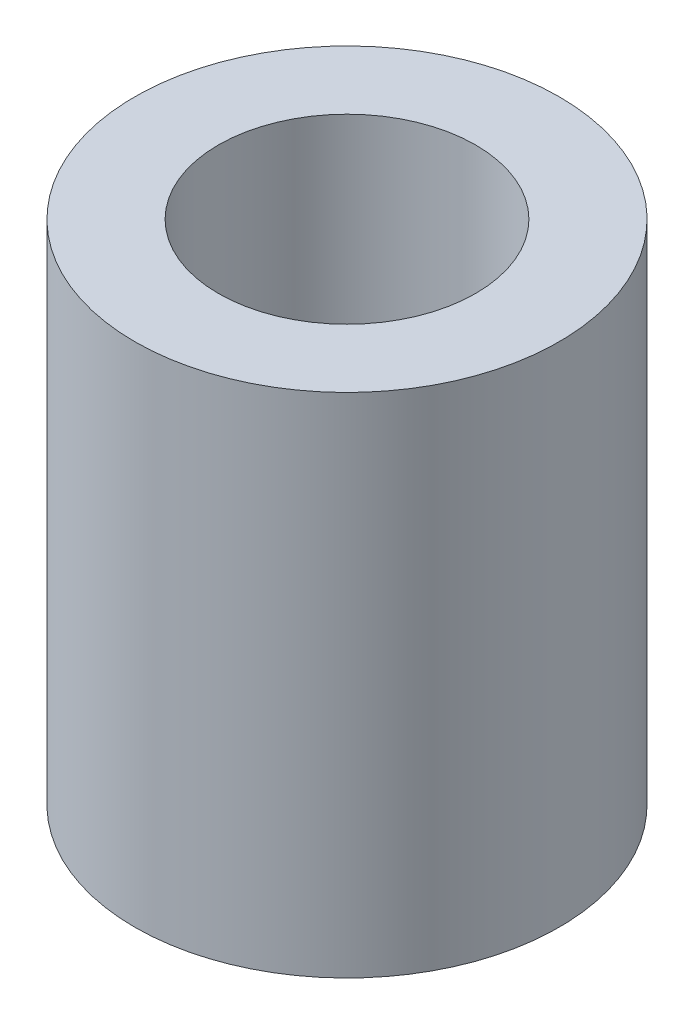
SolidWorks part; units mm, degrees
material "1060 Alloy"
ref_plane "Front Plane" through (0, 0, 0) normal (0, 0, 1) x (1, 0, 0)
ref_plane "Top Plane" through (0, 0, 0) normal (0, 1, 0) x (1, 0, 0)
ref_plane "Right Plane" through (0, 0, 0) normal (1, 0, 0) x (0, 0, -1)
sketch "Sketch1" plane through (0, 0, 0) normal (0, 1, 0) x (1, 0, 0)
  circle A0 centre (0, 0) radius 3.975
  dimension "D1" = 7.95
extrude "Boss-Extrude1" add sketch "Sketch1" along normal blind 9.5 contours A0
sketch "Sketch2" plane through (0, 9.5, 0) normal (0, 1, 0) x (1, 0, 0)
  circle A0 centre (0, 0) radius 2.41
  dimension "D1" = 4.82
extrude "Cut-Extrude1" cut sketch "Sketch2" against normal through all
